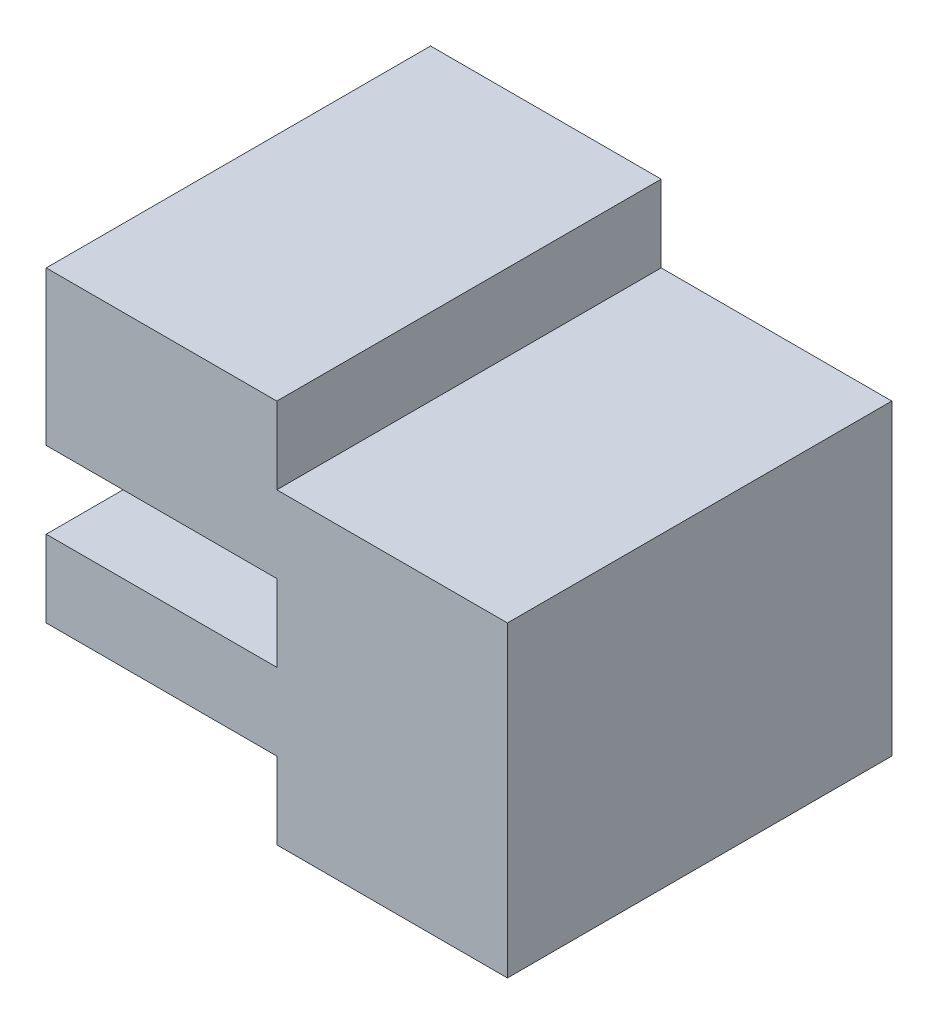
SolidWorks part; units mm, degrees
ref_plane "Front Plane" through (0, 0, 0) normal (0, 0, 1) x (1, 0, 0)
ref_plane "Top Plane" through (0, 0, 0) normal (0, 1, 0) x (1, 0, 0)
ref_plane "Right Plane" through (0, 0, 0) normal (1, 0, 0) x (0, 0, -1)
sketch "Sketch1" plane through (0, 0, 0) normal (0, 0, 1) x (1, 0, 0)
  line L0 (-30, 25) -> (-15, 25)
  line L1 (-15, 25) -> (-15, 20)
  line L2 (-15, 20) -> (0, 20)
  line L3 (0, 20) -> (0, 0)
  line L4 (0, 0) -> (-15, 0)
  line L5 (-15, 0) -> (-15, 5)
  line L6 (-15, 5) -> (-30, 5)
  line L7 (-30, 5) -> (-30, 10)
  line L8 (-30, 10) -> (-15, 10)
  line L9 (-15, 10) -> (-15, 15)
  line L10 (-15, 15) -> (-30, 15)
  line L11 (-30, 15) -> (-30, 25)
  dimension "D1" = 15
  dimension "D2" = 15
  dimension "D3" = 15
  dimension "D4" = 15
  dimension "D5" = 15
  dimension "D6" = 5
  dimension "D7" = 5
  dimension "D8" = 5
  dimension "D9" = 20
  dimension "D10" = 10
extrude "Boss-Extrude1" add sketch "Sketch1" along normal blind 25
